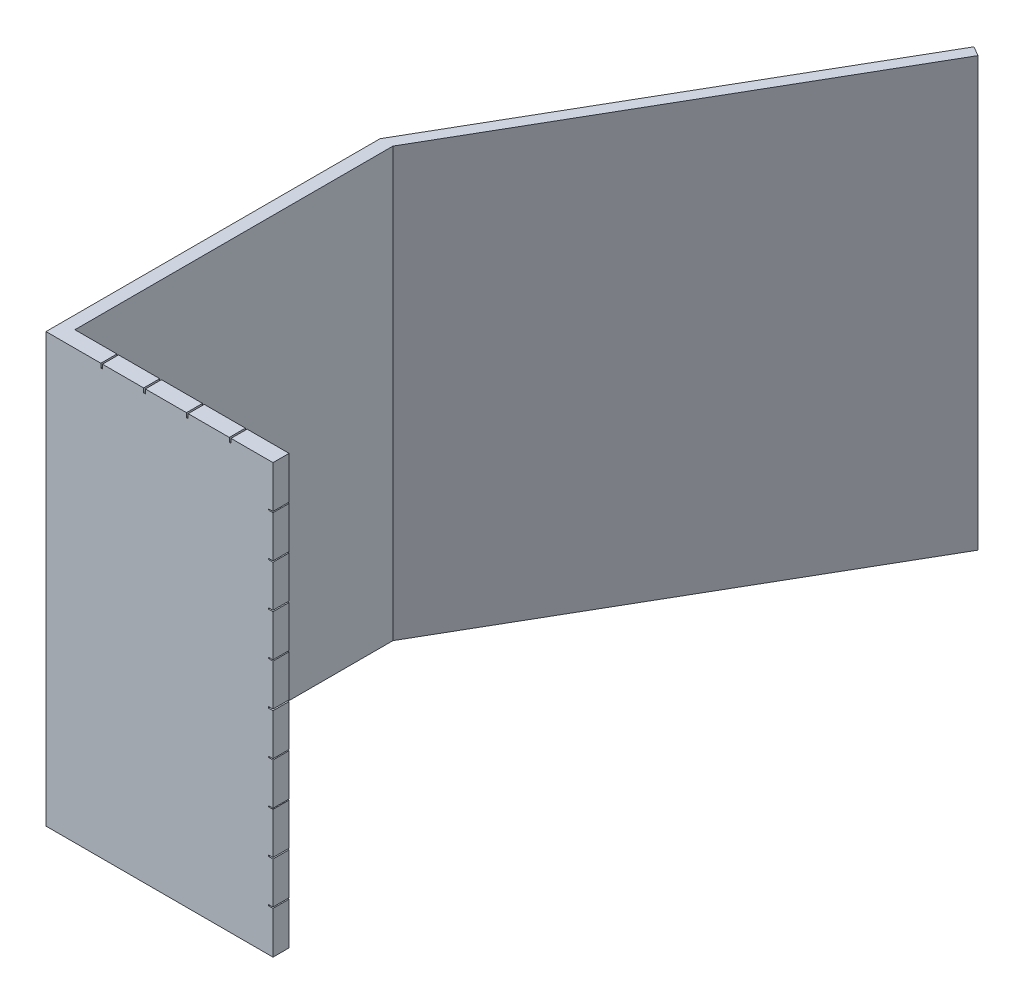
SolidWorks part; units mm, degrees
ref_plane "Front Plane" through (0, 0, 0) normal (0, 0, 1) x (1, 0, 0)
ref_plane "Top Plane" through (0, 0, 0) normal (0, 1, 0) x (1, 0, 0)
ref_plane "Right Plane" through (0, 0, 0) normal (1, 0, 0) x (0, 0, -1)
sketch "Sketch1" plane through (0, 0, 0) normal (0, 1, 0) x (1, 0, 0)
  line L3 (0.807, 30) -> (50.807, 116.6025)
  line L4 (50.807, 116.6025) -> (48.557, 117.9016)
  line L8 (-2.193, 0) -> (-2.193, 30)
  line L9 (-2.193, 30) -> (48.557, 117.9016)
  line L10 (0.807, 30) -> (0.807, 3.4233)
  line L11 (50.807, 116.6025) -> (50.807, -11.7875) construction
  line L14 (-2.193, 0) -> (-2.193, -48)
  line L15 (-2.193, -48) -> (50.807, -48)
  line L18 (0.807, -10) -> (0.807, 3.4233)
  line L19 (0.807, -10) -> (0.807, -44.2501)
  line L20 (0.807, -44.2501) -> (50.807, -44.2501)
  line L21 (50.807, -44.2501) -> (50.807, -48)
  dimension "D3" = 100
  dimension "D1" = 30
  dimension "D2" = 164.6025
  dimension "D4" = 78
  dimension "D5" = 53
extrude "Boss-Extrude1" add sketch "Sketch1" along normal blind 100
sketch "Sketch2" plane through (50.807, 0, 0) normal (1, 0, 0) x (0, 0, -1)
  line L0 (-48, 90) -> (-44.2501, 90) construction
  line L1 (-48, 100) -> (-48, 0) construction
  line L2 (-44.2501, 100) -> (-44.2501, 0) construction
  line L3 (-48, 80) -> (-44.2501, 80) construction
  line L4 (-44.2501, 100) -> (-44.2501, 0) construction
  line L5 (-48, 70) -> (-44.2501, 70) construction
  line L6 (-48, 60) -> (-44.2501, 60) construction
  line L7 (-48, 50) -> (-44.2501, 50) construction
  line L8 (-48, 40) -> (-44.2501, 40) construction
  line L9 (-48, 100) -> (-44.2501, 100) construction
  line L10 (-44.2501, 30) -> (-48, 30) construction
  line L11 (-44.2501, 20) -> (-48, 20) construction
  line L12 (-44.2501, 10) -> (-48, 10) construction
  line L13 (-46.125, 100) -> (-46.125, 0) construction
  line L14 (-48, 0) -> (-44.2501, 0) construction
  line L16 (-48, 89.8738) -> (-44.2501, 89.8738)
  line L17 (-48, 89.8738) -> (-48, 90.1262)
  line L18 (-48, 90.1262) -> (-44.2501, 90.1262)
  line L19 (-44.2501, 89.8738) -> (-44.2501, 90.1262)
  line L20 (-48, 89.8738) -> (-44.2501, 90.1262) construction
  line L21 (-48, 90.1262) -> (-44.2501, 89.8738) construction
  line L22 (-48, 79.8661) -> (-44.2501, 79.8661)
  line L23 (-48, 79.8661) -> (-48, 80.1339)
  line L24 (-48, 80.1339) -> (-44.2501, 80.1339)
  line L25 (-44.2501, 79.8661) -> (-44.2501, 80.1339)
  line L26 (-48, 79.8661) -> (-44.2501, 80.1339) construction
  line L27 (-48, 80.1339) -> (-44.2501, 79.8661) construction
  line L28 (-48, 69.8555) -> (-44.2501, 69.8555)
  line L29 (-48, 69.8555) -> (-48, 70.1445)
  line L30 (-48, 70.1445) -> (-44.2501, 70.1445)
  line L31 (-44.2501, 69.8555) -> (-44.2501, 70.1445)
  line L32 (-48, 69.8555) -> (-44.2501, 70.1445) construction
  line L33 (-48, 70.1445) -> (-44.2501, 69.8555) construction
  line L34 (-48, 59.8732) -> (-44.2501, 59.8732)
  line L35 (-48, 59.8732) -> (-48, 60.1268)
  line L36 (-48, 60.1268) -> (-44.2501, 60.1268)
  line L37 (-44.2501, 59.8732) -> (-44.2501, 60.1268)
  line L38 (-48, 59.8732) -> (-44.2501, 60.1268) construction
  line L39 (-48, 60.1268) -> (-44.2501, 59.8732) construction
  line L40 (-48, 49.8373) -> (-44.2501, 49.8373)
  line L41 (-48, 49.8373) -> (-48, 50.1627)
  line L42 (-48, 50.1627) -> (-44.2501, 50.1627)
  line L43 (-44.2501, 49.8373) -> (-44.2501, 50.1627)
  line L44 (-48, 49.8373) -> (-44.2501, 50.1627) construction
  line L45 (-48, 50.1627) -> (-44.2501, 49.8373) construction
  line L46 (-48, 39.8756) -> (-44.2501, 39.8756)
  line L47 (-48, 39.8756) -> (-48, 40.1244)
  line L48 (-48, 40.1244) -> (-44.2501, 40.1244)
  line L49 (-44.2501, 39.8756) -> (-44.2501, 40.1244)
  line L50 (-48, 39.8756) -> (-44.2501, 40.1244) construction
  line L51 (-48, 40.1244) -> (-44.2501, 39.8756) construction
  line L52 (-48, 29.8877) -> (-44.2501, 29.8877)
  line L53 (-48, 29.8877) -> (-48, 30.1123)
  line L54 (-48, 30.1123) -> (-44.2501, 30.1123)
  line L55 (-44.2501, 29.8877) -> (-44.2501, 30.1123)
  line L56 (-48, 29.8877) -> (-44.2501, 30.1123) construction
  line L57 (-48, 30.1123) -> (-44.2501, 29.8877) construction
  line L58 (-48, 19.8488) -> (-44.2501, 19.8488)
  line L59 (-48, 19.8488) -> (-48, 20.1512)
  line L60 (-48, 20.1512) -> (-44.2501, 20.1512)
  line L61 (-44.2501, 19.8488) -> (-44.2501, 20.1512)
  line L62 (-48, 19.8488) -> (-44.2501, 20.1512) construction
  line L63 (-48, 20.1512) -> (-44.2501, 19.8488) construction
  line L64 (-48, 9.8629) -> (-44.2501, 9.8629)
  line L65 (-48, 9.8629) -> (-48, 10.1371)
  line L66 (-48, 10.1371) -> (-44.2501, 10.1371)
  line L67 (-44.2501, 9.8629) -> (-44.2501, 10.1371)
  line L68 (-48, 9.8629) -> (-44.2501, 10.1371) construction
  line L69 (-48, 10.1371) -> (-44.2501, 9.8629) construction
  point P30 (-46.125, 90)
  point P35 (-46.125, 80)
  point P40 (-46.125, 70)
  point P45 (-46.125, 60)
  point P50 (-46.125, 50)
  point P55 (-46.125, 40)
  point P60 (-46.125, 30)
  point P65 (-46.125, 20)
  point P70 (-46.125, 10)
  dimension "D1" = 10
  dimension "D2" = 20
  dimension "D3" = 30
  dimension "D4" = 40
  dimension "D5" = 50
  dimension "D6" = 10
  dimension "D7" = 10
  dimension "D8" = 10
  dimension "D9" = 10
extrude "Cut-Extrude1" cut sketch "Sketch2" against normal blind 1
sketch "Sketch3" plane through (0, 100, 0) normal (0, 1, 0) x (1, 0, 0)
  line L0 (40.807, -44.2501) -> (40.807, -48) construction
  line L1 (50.807, -44.2501) -> (0.807, -44.2501) construction
  line L2 (-2.193, -48) -> (50.807, -48) construction
  line L3 (30.807, -44.2501) -> (30.807, -48) construction
  line L4 (20.807, -44.2501) -> (20.807, -48) construction
  line L5 (10.807, -44.2501) -> (10.807, -48) construction
  line L6 (50.807, -46.125) -> (-2.193, -46.125) construction
  line L7 (50.807, -48) -> (50.807, -44.2501) construction
  line L8 (-2.193, 30) -> (-2.193, -48) construction
  line L10 (40.6064, -48) -> (41.0077, -48)
  line L11 (40.6064, -48) -> (40.6064, -44.2501)
  line L12 (40.6064, -44.2501) -> (41.0077, -44.2501)
  line L13 (41.0077, -48) -> (41.0077, -44.2501)
  line L14 (40.6064, -48) -> (41.0077, -44.2501) construction
  line L15 (40.6064, -44.2501) -> (41.0077, -48) construction
  line L16 (30.6059, -48) -> (31.0082, -48)
  line L17 (30.6059, -48) -> (30.6059, -44.2501)
  line L18 (30.6059, -44.2501) -> (31.0082, -44.2501)
  line L19 (31.0082, -48) -> (31.0082, -44.2501)
  line L20 (30.6059, -48) -> (31.0082, -44.2501) construction
  line L21 (30.6059, -44.2501) -> (31.0082, -48) construction
  line L22 (20.6054, -48) -> (21.0087, -48)
  line L23 (20.6054, -48) -> (20.6054, -44.2501)
  line L24 (20.6054, -44.2501) -> (21.0087, -44.2501)
  line L25 (21.0087, -48) -> (21.0087, -44.2501)
  line L26 (20.6054, -48) -> (21.0087, -44.2501) construction
  line L27 (20.6054, -44.2501) -> (21.0087, -48) construction
  line L28 (10.6174, -48) -> (10.9967, -48)
  line L29 (10.6174, -48) -> (10.6174, -44.2501)
  line L30 (10.6174, -44.2501) -> (10.9967, -44.2501)
  line L31 (10.9967, -48) -> (10.9967, -44.2501)
  line L32 (10.6174, -48) -> (10.9967, -44.2501) construction
  line L33 (10.6174, -44.2501) -> (10.9967, -48) construction
  point P18 (40.807, -46.125)
  point P23 (30.807, -46.125)
  point P28 (20.807, -46.125)
  point P33 (10.807, -46.125)
  dimension "D1" = 10
  dimension "D2" = 10
  dimension "D3" = 10
  dimension "D4" = 10
extrude "Cut-Extrude2" cut sketch "Sketch3" against normal blind 1
